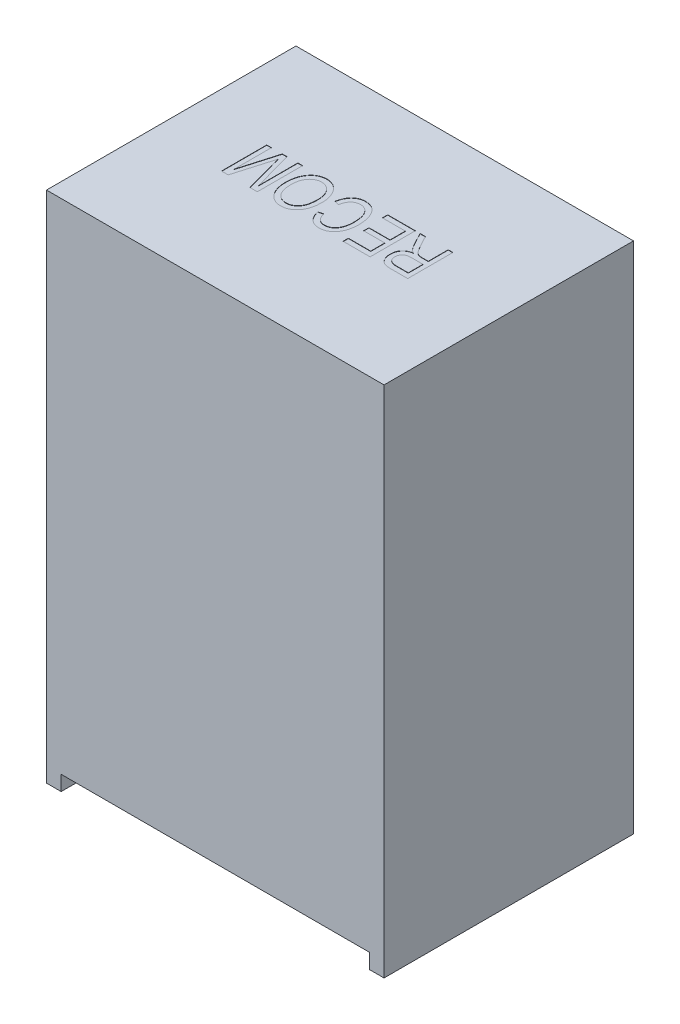
SolidWorks part; units mm, degrees
ref_plane "Front Plane" through (0, 0, 0) normal (0, 0, 1) x (1, 0, 0)
ref_plane "Top Plane" through (0, 0, 0) normal (0, 1, 0) x (1, 0, 0)
ref_plane "Right Plane" through (0, 0, 0) normal (1, 0, 0) x (0, 0, -1)
sketch "Sketch1" plane through (0, 0, 0) normal (0, 1, 0) x (1, 0, 0)
  line L1 (-5.75, -4.25) -> (5.75, -4.25)
  line L2 (-5.75, -4.25) -> (-5.75, 4.25)
  line L3 (-5.75, 4.25) -> (5.75, 4.25)
  line L4 (5.75, -4.25) -> (5.75, 4.25)
  line L5 (-5.75, -4.25) -> (5.75, 4.25) construction
  line L6 (-5.75, 4.25) -> (5.75, -4.25) construction
  point P0 (0, 0)
  dimension "D1" = 11.5
  dimension "D2" = 8.5
extrude "Boss-Extrude1" add sketch "Sketch1" along normal blind 17.5
sketch "Sketch2" plane through (0, 0, 0) normal (0, -1, 0) x (1, 0, 0)
  line L0 (-5.75, 4.25) -> (5.75, 4.25) construction
  line L1 (-5.25, -4.25) -> (5.25, -4.25)
  line L2 (-5.25, -4.25) -> (-5.25, 4.25)
  line L3 (-5.25, 4.25) -> (5.25, 4.25)
  line L4 (5.25, -4.25) -> (5.25, 4.25)
  line L5 (-5.25, -4.25) -> (5.25, 4.25) construction
  line L6 (-5.25, 4.25) -> (5.25, -4.25) construction
  line L7 (-5.75, -4.25) -> (-5.75, 4.25) construction
  point P0 (0, 0)
  dimension "D1" = 0.5
extrude "Cut-Extrude1" cut sketch "Sketch2" against normal blind 0.51
ref_plane "Pin Plane" through (0, 0, 2.25) normal (0, 0, 1) x (1, 0, 0)
sketch "Sketch4" plane through (0, 0, -4.25) normal (0, 0, -1) x (-1, 0, 0)
  line L1 (0, 4.675) -> (0, -4.675) construction
  line L2 (5.25, 0.51) -> (-5.25, 0.51) construction
  circle A0 centre (-2.54, 1.51) radius 0.5
  point P6 (0, 0)
  dimension "D1" = 1
  dimension "D2" = 2.54
  dimension "D3" = 1
extrude "Cut-Extrude3" cut sketch "Sketch4" against normal blind 0.01
sketch "Sketch5" plane through (0, 17.5, 0) normal (0, 1, 0) x (1, 0, 0)
  line L0 (3.1558, 0.832) -> (-3.8998, 0.832) construction
  text T0 "RECOM" font "Arial Narrow" height in points 6
extrude "Cut-Extrude4" cut sketch "Sketch5" against normal blind 0.01
